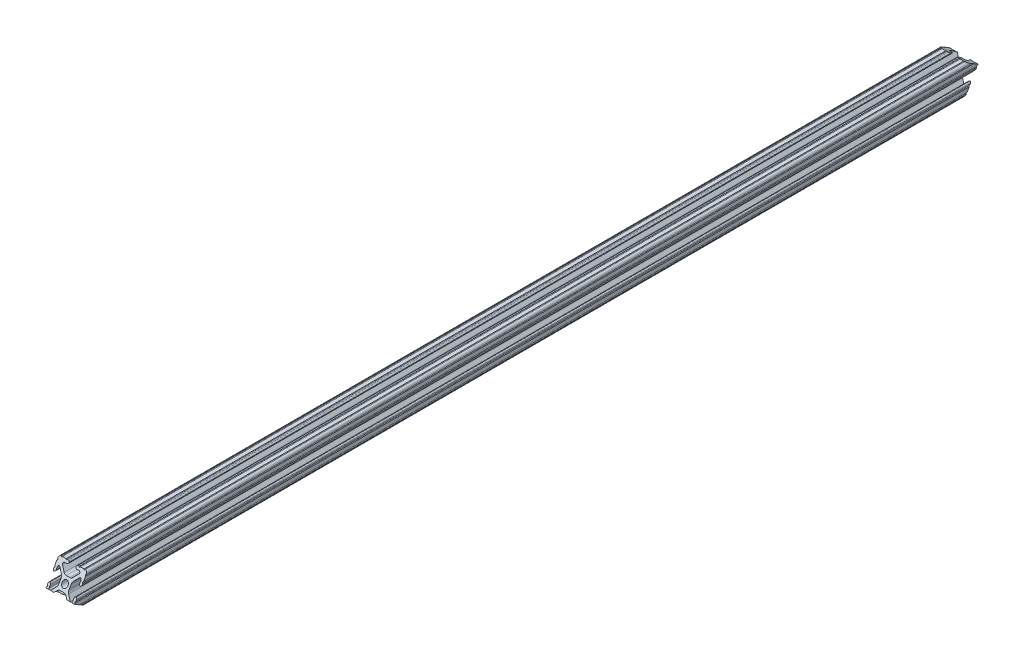
SolidWorks part; units mm, degrees
ref_plane "Front Plane" through (0, 0, 0) normal (0, 0, 1) x (1, 0, 0)
ref_plane "Top Plane" through (0, 0, 0) normal (0, 1, 0) x (1, 0, 0)
ref_plane "Right Plane" through (0, 0, 0) normal (1, 0, 0) x (0, 0, -1)
sketch "Sketch1" plane through (0, 0, 0) normal (0, 0, 1) x (1, 0, 0)
  line L88 (-7.1797, -8.6452) -> (-3.9523, -5.4237)
  line L89 (-1.7093, -4.4958) -> (1.7093, -4.4958)
  line L90 (3.9523, -5.4237) -> (7.1797, -8.6452)
  line L91 (6.4164, -10.4902) -> (4.2875, -10.4902)
  line L92 (3.2385, -11.5392) -> (3.2385, -11.651)
  line L93 (4.2875, -12.7) -> (5.3171, -12.7)
  line L94 (6.3331, -12.7) -> (9.5504, -12.7)
  line L95 (12.7, -9.5504) -> (12.7, -6.3331)
  line L96 (12.7, -5.3171) -> (12.7, -4.2875)
  line L97 (11.651, -3.2385) -> (11.5392, -3.2385)
  line L98 (10.4902, -4.2875) -> (10.4902, -6.4021)
  line L99 (8.7371, -7.1294) -> (5.441, -3.8408)
  line L100 (4.5085, -1.5932) -> (4.5085, 1.5932)
  line L101 (5.441, 3.8408) -> (8.7371, 7.1294)
  line L102 (10.4902, 6.4021) -> (10.4902, 4.2875)
  line L103 (11.5392, 3.2385) -> (11.651, 3.2385)
  line L104 (12.7, 4.2875) -> (12.7, 5.3171)
  line L105 (12.7, 6.3331) -> (12.7, 9.5504)
  line L106 (9.5504, 12.7) -> (6.3331, 12.7)
  line L107 (5.3171, 12.7) -> (4.2875, 12.7)
  line L108 (3.2385, 11.651) -> (3.2385, 11.5392)
  line L109 (4.2875, 10.4902) -> (6.4768, 10.4902)
  line L110 (7.207, 8.7244) -> (3.8983, 5.4232)
  line L111 (1.6558, 4.4958) -> (-1.6558, 4.4958)
  line L112 (-3.8983, 5.4232) -> (-7.207, 8.7244)
  line L113 (-6.4768, 10.4902) -> (-4.2875, 10.4902)
  line L114 (-3.2385, 11.5392) -> (-3.2385, 11.651)
  line L115 (-4.2875, 12.7) -> (-5.3171, 12.7)
  line L116 (-6.3331, 12.7) -> (-9.5504, 12.7)
  line L117 (-12.7, 9.5504) -> (-12.7, 6.3331)
  line L118 (-12.7, 5.3171) -> (-12.7, 4.2875)
  line L119 (-11.651, 3.2385) -> (-11.5392, 3.2385)
  line L120 (-10.4902, 4.2875) -> (-10.4902, 6.4021)
  line L121 (-8.7371, 7.1294) -> (-5.441, 3.8408)
  line L122 (-4.5085, 1.5932) -> (-4.5085, -1.5932)
  line L123 (-5.441, -3.8408) -> (-8.7371, -7.1294)
  line L124 (-10.4902, -6.4021) -> (-10.4902, -4.2875)
  line L125 (-11.5392, -3.2385) -> (-11.651, -3.2385)
  line L126 (-12.7, -4.2875) -> (-12.7, -5.3171)
  line L127 (-12.7, -6.3331) -> (-12.7, -9.5504)
  line L128 (-9.5504, -12.7) -> (-6.3331, -12.7)
  line L129 (-5.3171, -12.7) -> (-4.2875, -12.7)
  line L130 (-3.2385, -11.651) -> (-3.2385, -11.5392)
  line L131 (-4.2875, -10.4902) -> (-6.4164, -10.4902)
  circle A1 centre (0, 0) radius 2.6035
  arc A104 (-7.1797, -8.6452) -> (-6.4164, -10.4902) centre (-6.4164, -9.4098) ccw
  arc A105 (-1.7093, -4.4958) -> (-3.9523, -5.4237) centre (-1.7093, -7.6708) ccw
  arc A106 (3.9523, -5.4237) -> (1.7093, -4.4958) centre (1.7093, -7.6708) ccw
  arc A107 (6.4164, -10.4902) -> (7.1797, -8.6452) centre (6.4164, -9.4098) ccw
  arc A108 (4.2875, -10.4902) -> (3.2385, -11.5392) centre (4.2875, -11.5392) ccw
  arc A109 (3.2385, -11.651) -> (4.2875, -12.7) centre (4.2875, -11.651) ccw
  arc A110 (6.3331, -12.7) -> (5.3171, -12.7) centre (5.8251, -12.7) ccw
  arc A111 (10.5664, -12.6998) -> (9.5504, -12.7) centre (10.0584, -12.7) ccw
  arc A112 (10.5664, -12.6998) -> (12.6998, -10.5664) centre (10.5918, -10.5918) ccw
  arc A113 (12.7, -9.5504) -> (12.6998, -10.5664) centre (12.7, -10.0584) ccw
  arc A114 (12.7, -5.3171) -> (12.7, -6.3331) centre (12.7, -5.8251) ccw
  arc A115 (12.7, -4.2875) -> (11.651, -3.2385) centre (11.651, -4.2875) ccw
  arc A116 (11.5392, -3.2385) -> (10.4902, -4.2875) centre (11.5392, -4.2875) ccw
  arc A117 (8.7371, -7.1294) -> (10.4902, -6.4021) centre (9.4628, -6.4021) ccw
  arc A118 (4.5085, -1.5932) -> (5.441, -3.8408) centre (7.6835, -1.5932) ccw
  arc A119 (5.441, 3.8408) -> (4.5085, 1.5932) centre (7.6835, 1.5932) ccw
  arc A120 (10.4902, 6.4021) -> (8.7371, 7.1294) centre (9.4628, 6.4021) ccw
  arc A121 (10.4902, 4.2875) -> (11.5392, 3.2385) centre (11.5392, 4.2875) ccw
  arc A122 (11.651, 3.2385) -> (12.7, 4.2875) centre (11.651, 4.2875) ccw
  arc A123 (12.7, 6.3331) -> (12.7, 5.3171) centre (12.7, 5.8251) ccw
  arc A124 (12.6998, 10.5664) -> (12.7, 9.5504) centre (12.7, 10.0584) ccw
  arc A125 (12.6998, 10.5664) -> (10.5664, 12.6998) centre (10.5918, 10.5918) ccw
  arc A126 (9.5504, 12.7) -> (10.5664, 12.6998) centre (10.0584, 12.7) ccw
  arc A127 (5.3171, 12.7) -> (6.3331, 12.7) centre (5.8251, 12.7) ccw
  arc A128 (4.2875, 12.7) -> (3.2385, 11.651) centre (4.2875, 11.651) ccw
  arc A129 (3.2385, 11.5392) -> (4.2875, 10.4902) centre (4.2875, 11.5392) ccw
  arc A130 (7.207, 8.7244) -> (6.4768, 10.4902) centre (6.4768, 9.4563) ccw
  arc A131 (1.6558, 4.4958) -> (3.8983, 5.4232) centre (1.6558, 7.6708) ccw
  arc A132 (-3.8983, 5.4232) -> (-1.6558, 4.4958) centre (-1.6558, 7.6708) ccw
  arc A133 (-6.4768, 10.4902) -> (-7.207, 8.7244) centre (-6.4768, 9.4563) ccw
  arc A134 (-4.2875, 10.4902) -> (-3.2385, 11.5392) centre (-4.2875, 11.5392) ccw
  arc A135 (-3.2385, 11.651) -> (-4.2875, 12.7) centre (-4.2875, 11.651) ccw
  arc A136 (-6.3331, 12.7) -> (-5.3171, 12.7) centre (-5.8251, 12.7) ccw
  arc A137 (-10.5664, 12.6998) -> (-9.5504, 12.7) centre (-10.0584, 12.7) ccw
  arc A138 (-10.5664, 12.6998) -> (-12.6998, 10.5664) centre (-10.5918, 10.5918) ccw
  arc A139 (-12.7, 9.5504) -> (-12.6998, 10.5664) centre (-12.7, 10.0584) ccw
  arc A140 (-12.7, 5.3171) -> (-12.7, 6.3331) centre (-12.7, 5.8251) ccw
  arc A141 (-12.7, 4.2875) -> (-11.651, 3.2385) centre (-11.651, 4.2875) ccw
  arc A142 (-11.5392, 3.2385) -> (-10.4902, 4.2875) centre (-11.5392, 4.2875) ccw
  arc A143 (-8.7371, 7.1294) -> (-10.4902, 6.4021) centre (-9.4628, 6.4021) ccw
  arc A144 (-4.5085, 1.5932) -> (-5.441, 3.8408) centre (-7.6835, 1.5932) ccw
  arc A145 (-5.441, -3.8408) -> (-4.5085, -1.5932) centre (-7.6835, -1.5932) ccw
  arc A146 (-10.4902, -6.4021) -> (-8.7371, -7.1294) centre (-9.4628, -6.4021) ccw
  arc A147 (-10.4902, -4.2875) -> (-11.5392, -3.2385) centre (-11.5392, -4.2875) ccw
  arc A148 (-11.651, -3.2385) -> (-12.7, -4.2875) centre (-11.651, -4.2875) ccw
  arc A149 (-12.7, -6.3331) -> (-12.7, -5.3171) centre (-12.7, -5.8251) ccw
  arc A150 (-12.6998, -10.5664) -> (-12.7, -9.5504) centre (-12.7, -10.0584) ccw
  arc A151 (-12.6998, -10.5664) -> (-10.5664, -12.6998) centre (-10.5918, -10.5918) ccw
  arc A152 (-9.5504, -12.7) -> (-10.5664, -12.6998) centre (-10.0584, -12.7) ccw
  arc A153 (-5.3171, -12.7) -> (-6.3331, -12.7) centre (-5.8251, -12.7) ccw
  arc A154 (-4.2875, -12.7) -> (-3.2385, -11.651) centre (-4.2875, -11.651) ccw
  arc A155 (-3.2385, -11.5392) -> (-4.2875, -10.4902) centre (-4.2875, -11.5392) ccw
extrude "Boss-Extrude1" add sketch "Sketch1" along normal mid plane 806.45
sketch "Sketch2" plane through (0, 0, 0) normal (1, 0, 0) x (0, 0, -1)
  line L0 (0, 0) -> (0, 70.3074) construction
  line L1 (-403.225, -12.6998) -> (-388.5605, 12.6998)
  line L2 (-403.225, 12.6998) -> (403.225, 12.6998) construction
  line L4 (-403.225, 12.6998) -> (-403.225, -12.6998)
  line L8 (403.225, -12.6998) -> (403.225, 12.6998)
  line L14 (-403.225, 12.6998) -> (-403.225, 30.6758)
  line L15 (-403.225, 30.6758) -> (-388.5605, 30.6758)
  line L16 (-388.5605, 30.6758) -> (-388.5605, 12.6998)
  line L17 (406.4, 0) -> (478.5617, 0) construction
  line L18 (391.7355, -24.3912) -> (381.8114, -24.3896)
  line L19 (403.225, -24.3912) -> (391.7355, -24.3912)
  line L20 (403.225, -12.6998) -> (403.225, -24.3912)
  line L21 (381.8114, -24.3896) -> (403.225, 12.6998)
  point P12 (381.8114, -24.3912)
  point P15 (403.225, -24.3912)
  dimension "D1" = 30
  dimension "D2" = 30
extrude "30 Deg End Trim" cut sketch "Sketch2" against normal through all and the other way through all
sketch "Sketch3" plane through (0, 0, 0) normal (1, 0, 0) x (0, 0, -1)
  line L2 (-402.4313, -5.8258) -> (-423.0778, -5.8258)
  line L5 (-406.4, -12.6998) -> (-384.403, -25.3998) construction
  line L6 (-406.4, -12.6998) -> (-402.4313, -5.8258) construction
  line L7 (-403.225, -12.6998) -> (-393.2971, 4.4958) construction
  line L8 (-402.4313, -5.8258) -> (-380.4342, -18.5258)
  line L9 (-384.403, -25.3998) -> (-380.4342, -18.5258)
  line L10 (-423.0778, -5.8258) -> (-423.0778, -25.3998)
  line L11 (-423.0778, -25.3998) -> (-384.403, -25.3998)
  line L12 (402.4313, 5.8258) -> (411.2633, 0.7266)
  line L13 (406.4, 12.6998) -> (384.403, 25.3998) construction
  line L14 (406.4, 12.6998) -> (402.4313, 5.8258) construction
  line L15 (402.4313, 5.8258) -> (380.4342, 18.5258)
  line L16 (384.403, 25.3998) -> (380.4342, 18.5258)
  line L17 (411.2633, 0.7266) -> (422.9015, 20.8845)
  line L18 (422.9015, 20.8845) -> (384.403, 25.3998)
  dimension "D1" = 7.9375
  dimension "D2" = 25.4
  dimension "D3" = 25.4
  dimension "D4" = 7.9375
extrude "Trim to Fit" cut sketch "Sketch3" against normal through all and the other way through all
